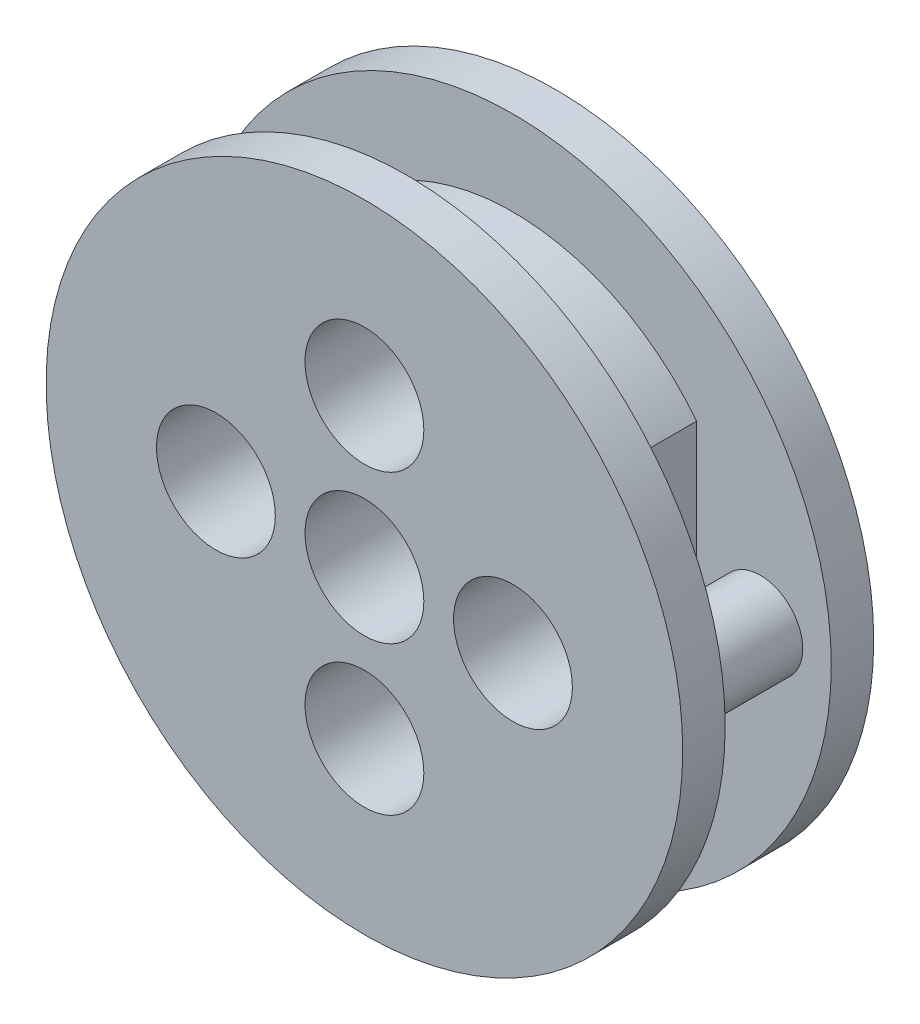
SolidWorks part; units mm, degrees
ref_plane "前视基准面" through (0, 0, 0) normal (0, 0, 1) x (1, 0, 0)
ref_plane "上视基准面" through (0, 0, 0) normal (0, 1, 0) x (1, 0, 0)
ref_plane "右视基准面" through (0, 0, 0) normal (1, 0, 0) x (0, 0, -1)
sketch "草图1" plane through (0, 0, 0) normal (0, 0, 1) x (1, 0, 0)
  circle A0 centre (0, 0) radius 15
extrude "凸台-拉伸1" add sketch "草图1" along normal blind 2
sketch "草图2" plane through (0, 0, 2) normal (0, 0, 1) x (1, 0, 0)
  line L0 (-9.8736, 0) -> (12.1264, 0) construction
  line L1 (0, 11) -> (0, -11) construction
  line L2 (8.6559, 6.7879) -> (8.6559, -6.7879)
  arc A0 (8.6559, 6.7879) -> (8.6559, -6.7879) centre (0, 0) ccw
  circle A1 centre (11.6559, 0) radius 2
  point P10 (8.6559, 0)
  dimension "D1" = 3
extrude "凸台-拉伸2" add sketch "草图2" along normal blind 5
sketch "草图3" plane through (0, 0, 7) normal (0, 0, 1) x (1, 0, 0)
  circle A0 centre (0, 0) radius 15
extrude "凸台-拉伸3" add sketch "草图3" along normal blind 2
sketch "草图4" plane through (0, 0, 0) normal (0, 0, -1) x (-1, 0, 0)
  line L0 (-15, 0) -> (15, 0) construction
  line L1 (0, -15) -> (0, 15) construction
  circle A0 centre (0, 7) radius 1.5
  circle A1 centre (0, 0) radius 15 construction
  circle A2 centre (0, -7) radius 1.5
  circle A3 centre (7, 0) radius 1.5
  circle A4 centre (-7, 0) radius 1.5
  circle A5 centre (0, 0) radius 2.8
  dimension "D1" = 7
  dimension "D2" = 7
extrude "切除-拉伸1" cut sketch "草图4" against normal up to next
sketch "草图5" plane through (0, 0, 9) normal (0, 0, 1) x (1, 0, 0)
  circle A0 centre (0, 7) radius 2.8
  circle A1 centre (7, 0) radius 2.8
  circle A2 centre (-7, 0) radius 2.8
  circle A3 centre (0, -7) radius 2.8
extrude "切除-拉伸2" cut sketch "草图5" against normal blind 5
